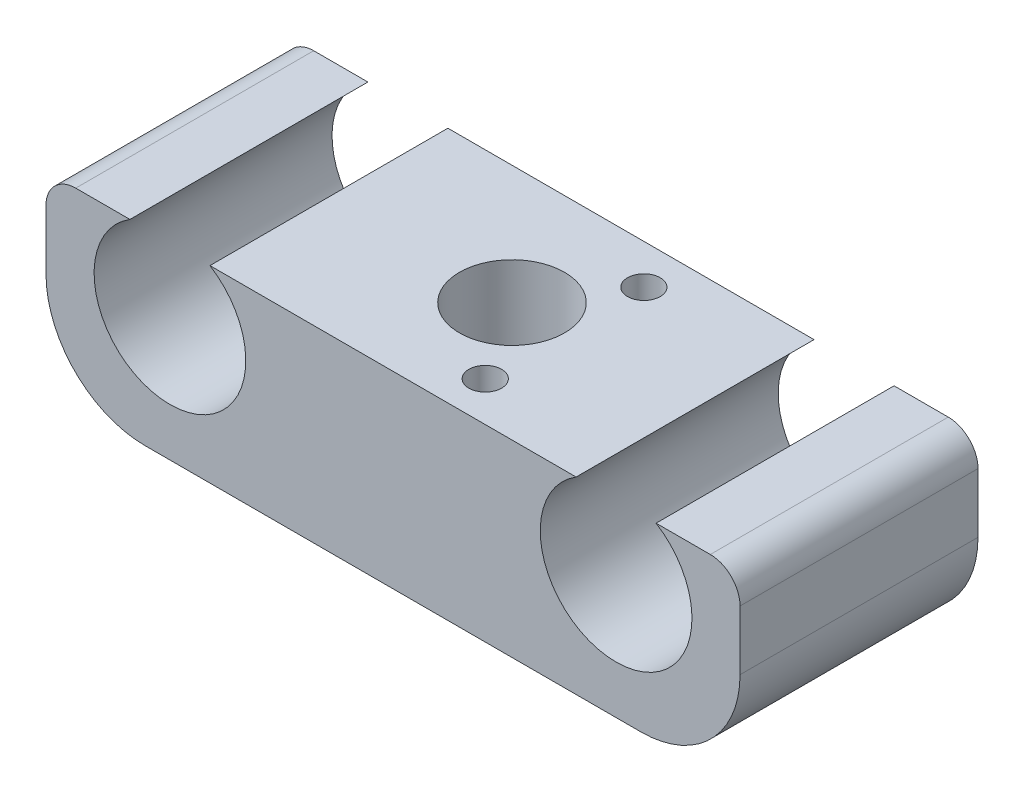
SolidWorks part; units mm, degrees
ref_plane "前视基准面" through (0, 0, 0) normal (0, 0, 1) x (1, 0, 0)
ref_plane "上视基准面" through (0, 0, 0) normal (0, 1, 0) x (1, 0, 0)
ref_plane "右视基准面" through (0, 0, 0) normal (1, 0, 0) x (0, 0, -1)
sketch "草图1" plane through (0, 0, 0) normal (0, 0, 1) x (1, 0, 0)
  line L0 (0, 0) -> (70, 0)
  line L1 (0, 0) -> (0, 19)
  line L2 (0, 19) -> (70, 19)
  line L3 (70, 19) -> (70, 0)
extrude "凸台-拉伸1" add sketch "草图1" along normal blind 24
sketch "草图2" plane through (0, 0, 24) normal (0, 0, 1) x (1, 0, 0)
  circle A0 centre (57.5, 12.5) radius 7.65
  circle A1 centre (12.5, 12.5) radius 7.65
extrude "切除-拉伸1" cut sketch "草图2" against normal blind 24
sketch "草图3" plane through (0, 0, 0) normal (0, -1, 0) x (1, 0, 0)
  circle A0 centre (35, 12) radius 5.3
extrude "切除-拉伸2" cut sketch "草图3" against normal blind 24
fillet "圆角1" radius 10 1 edges at (0, 0, 12)
fillet "圆角4" radius 3 1 edges at (0, 19, 12)
fillet "圆角5" radius 10 1 edges at (70, 0, 12)
fillet "圆角6" radius 3 1 edges at (70, 19, 12)
sketch "草图4" plane through (0, 19, 0) normal (0, 1, 0) x (1, 0, 0)
  circle A1 centre (40.3, -20) radius 1.65
  circle A2 centre (40.3, -4) radius 1.65
extrude "切除-拉伸3" cut sketch "草图4" against normal blind 24
